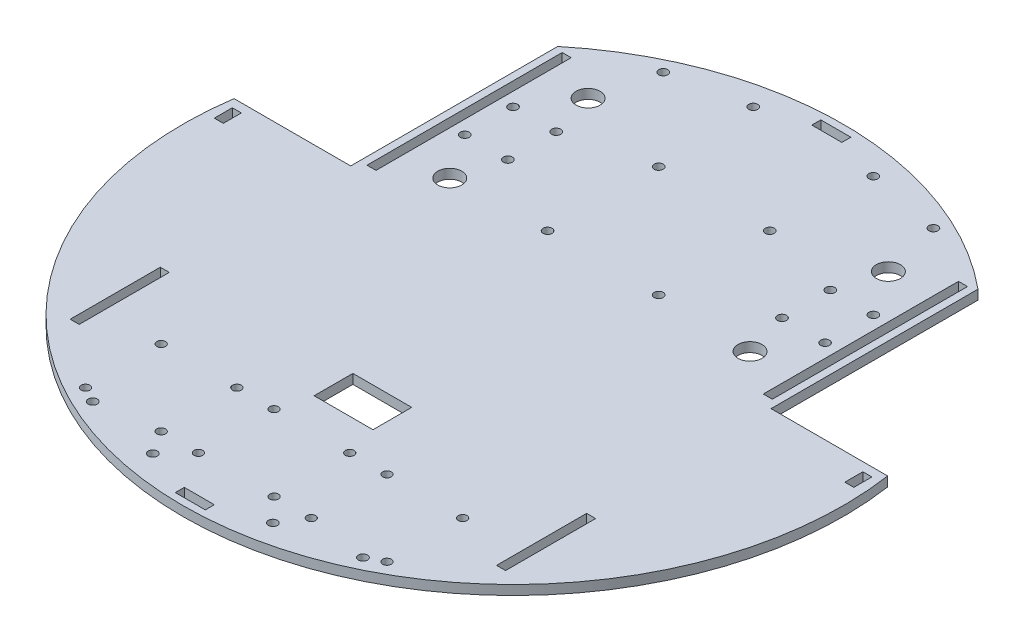
SolidWorks part; units mm, degrees
ref_plane "前视基准面" through (0, 0, 0) normal (0, 0, 1) x (1, 0, 0)
ref_plane "上视基准面" through (0, 0, 0) normal (0, 1, 0) x (1, 0, 0)
ref_plane "右视基准面" through (0, 0, 0) normal (1, 0, 0) x (0, 0, -1)
sketch "草图1" plane through (0, 0, 0) normal (0, 1, 0) x (1, 0, 0)
  line L0 (0, 0) -> (109.026, 0) construction
  line L5 (0, 0) -> (0, 50.562) construction
  line L6 (-5, -104.5) -> (5, -104.5)
  line L13 (-9.8, -43.55) -> (9.8, -43.55)
  line L14 (-9.8, -43.55) -> (-9.8, -56.45)
  line L15 (-9.8, -56.45) -> (9.8, -56.45)
  line L16 (9.8, -43.55) -> (9.8, -56.45)
  line L17 (-9.8, -43.55) -> (9.8, -56.45) construction
  line L18 (-9.8, -56.45) -> (9.8, -43.55) construction
  line L19 (-108.8419, 15.92) -> (-70, 15.92)
  line L20 (-70, 84.8528) -> (-70, 15.92)
  line L21 (108.8419, 15.92) -> (70, 15.92)
  line L22 (70, 84.8528) -> (70, 15.92)
  line L23 (-5, 107.5) -> (5, 107.5)
  line L24 (-5, 107.5) -> (-5, 104.5)
  line L25 (-5, 104.5) -> (5, 104.5)
  line L26 (5, 107.5) -> (5, 104.5)
  line L27 (-5, 107.5) -> (5, 104.5) construction
  line L28 (-5, 104.5) -> (5, 107.5) construction
  line L29 (5, -107.5) -> (5, -104.5)
  line L30 (-5, -107.5) -> (5, -107.5)
  line L31 (-5, -107.5) -> (-5, -104.5)
  line L32 (106.5, 7) -> (103.5, 7)
  line L33 (-106.5, 13) -> (-103.5, 13)
  line L34 (-106.5, 13) -> (-106.5, 7)
  line L35 (-106.5, 7) -> (-103.5, 7)
  line L36 (-103.5, 13) -> (-103.5, 7)
  line L37 (-106.5, 13) -> (-103.5, 7) construction
  line L38 (-106.5, 7) -> (-103.5, 13) construction
  line L39 (103.5, 13) -> (103.5, 7)
  line L40 (106.5, 13) -> (103.5, 13)
  line L41 (106.5, 13) -> (106.5, 7)
  line L42 (67.5, 18.8528) -> (64.5, 18.8528)
  line L43 (-67.5, 83.8528) -> (-64.5, 83.8528)
  line L44 (-67.5, 83.8528) -> (-67.5, 18.8528)
  line L45 (-67.5, 18.8528) -> (-64.5, 18.8528)
  line L46 (-64.5, 83.8528) -> (-64.5, 18.8528)
  line L47 (-67.5, 83.8528) -> (-64.5, 18.8528) construction
  line L48 (-67.5, 18.8528) -> (-64.5, 83.8528) construction
  line L49 (64.5, 83.8528) -> (64.5, 18.8528)
  line L50 (67.5, 83.8528) -> (64.5, 83.8528)
  line L51 (67.5, 83.8528) -> (67.5, 18.8528)
  line L52 (72.5, -45) -> (69.5, -45)
  line L53 (-72.5, -75) -> (-69.5, -75)
  line L54 (-72.5, -75) -> (-72.5, -45)
  line L55 (-72.5, -45) -> (-69.5, -45)
  line L56 (-69.5, -75) -> (-69.5, -45)
  line L57 (-72.5, -75) -> (-69.5, -45) construction
  line L58 (-72.5, -45) -> (-69.5, -75) construction
  line L59 (69.5, -75) -> (69.5, -45)
  line L60 (72.5, -75) -> (69.5, -75)
  line L61 (72.5, -75) -> (72.5, -45)
  circle A8 centre (-60, 43.92) radius 1.5
  circle A9 centre (-60, 60) radius 1.5
  circle A10 centre (-45.65, 60) radius 1.5
  circle A11 centre (-45.65, 43.92) radius 1.5
  circle A12 centre (60, 60) radius 1.5
  circle A13 centre (45.65, 60) radius 1.5
  circle A14 centre (45.65, 43.92) radius 1.5
  circle A15 centre (60, 43.92) radius 1.5
  circle A24 centre (-20, -100) radius 1.5
  circle A25 centre (20, -100) radius 1.5
  circle A26 centre (20, 100) radius 1.5
  circle A27 centre (-20, 100) radius 1.5
  circle A30 centre (-50, 75) radius 4
  circle A31 centre (50, 75) radius 4
  circle A36 centre (-18.5, 67) radius 1.5
  circle A39 centre (-18.5, 30) radius 1.5
  arc A40 (-108.8419, 15.92) -> (108.8419, 15.92) centre (0, 0) ccw
  circle A41 centre (18.5, 30) radius 1.5
  circle A42 centre (18.5, 67) radius 1.5
  circle A43 centre (-12.6, -67) radius 1.45
  circle A44 centre (-12.6, -92.2) radius 1.45
  circle A45 centre (12.6, -92.2) radius 1.45
  circle A46 centre (12.6, -67) radius 1.45
  circle A47 centre (-45, 95) radius 1.5
  circle A48 centre (45, 95) radius 1.5
  circle A49 centre (45, -95) radius 1.5
  circle A50 centre (-45, -95) radius 1.5
  circle A51 centre (-50.2, -67) radius 1.45
  circle A52 centre (-50.2, -92.2) radius 1.45
  circle A53 centre (-25, -67) radius 1.45
  circle A54 centre (-25, -92.2) radius 1.45
  circle A55 centre (50.2, -92.2) radius 1.45
  circle A56 centre (25, -92.2) radius 1.45
  circle A57 centre (25, -67) radius 1.45
  circle A58 centre (50.2, -67) radius 1.45
  circle A59 centre (-50, 28.92) radius 4
  circle A60 centre (50, 28.92) radius 4
  arc A61 (70, 84.8528) -> (-70, 84.8528) centre (0, 0) ccw
  point P0 (0, 0)
  point P43 (-110, 0)
  point P74 (0, -50)
  point P81 (0, 106)
  point P96 (-105, 10)
  point P109 (-66, 51.3528)
  point P119 (-71, -60)
  dimension "D3" = 14.35
  dimension "D4" = 16.08
  dimension "D6" = 3
  dimension "D8" = 220
  dimension "D9" = 8
  dimension "D10" = 100
  dimension "D15" = 3
  dimension "D17" = 2.9
  dimension "D22" = 50
  dimension "D24" = 95
  dimension "D11" = 3
  dimension "D25" = 3
  dimension "D26" = 17
  dimension "D30" = 25
  dimension "D35" = 3
  dimension "D5" = 60
  dimension "D7" = 50
  dimension "D12" = 37
  dimension "D13" = 37
  dimension "D14" = 100
  dimension "D16" = 20
  dimension "D18" = 25.2
  dimension "D19" = 19.6
  dimension "D20" = 12.9
  dimension "D21" = 25.2
  dimension "D23" = 45
  dimension "D27" = 30
  dimension "D28" = 15
  dimension "D29" = 25.2
  dimension "D31" = 10
  dimension "D32" = 10
  dimension "D33" = 28
  dimension "D34" = 15
  dimension "D36" = 106
  dimension "D37" = 3
  dimension "D38" = 6
  dimension "D39" = 10
  dimension "D40" = 105
  dimension "D41" = 65
  dimension "D42" = 3
  dimension "D43" = 6
  dimension "D44" = 1
  dimension "D45" = 3
  dimension "D46" = 30
  dimension "D47" = 60
extrude "Base" add sketch "草图1" along normal blind 3.175
